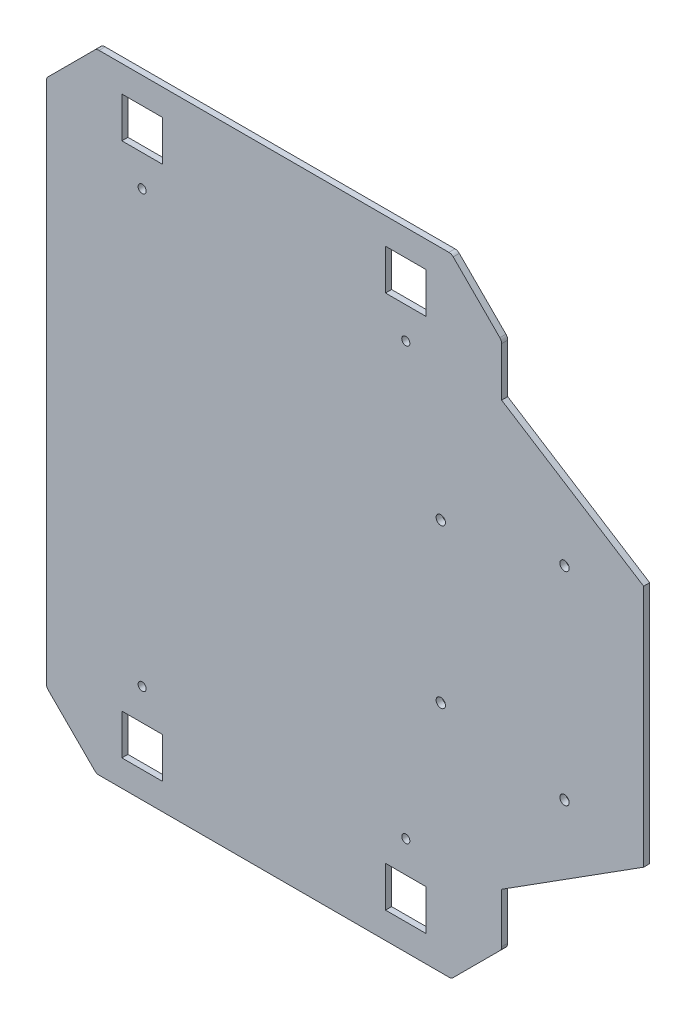
SolidWorks part; units mm, degrees
material "Pin"
ref_plane "Plan de dessus" through (0, 0, 0) normal (0, 0, 1) x (1, 0, 0)
ref_plane "Plan de droite" through (0, 0, 0) normal (0, 1, 0) x (1, 0, 0)
ref_plane "Plan de face" through (0, 0, 0) normal (1, 0, 0) x (0, 0, -1)
sketch "Esquisse1" plane through (0, 0, 0) normal (0, 0, 1) x (1, 0, 0)
  line L0 (0, 0) -> (-175, 0)
  line L1 (-175, 0) -> (-199.7487, 24.7487)
  line L2 (-199.7487, 24.7487) -> (-199.7487, 284.7487)
  line L3 (-199.7487, 284.7487) -> (-175, 309.4975)
  line L4 (-175, 309.4975) -> (0, 309.4975)
  line L5 (0, 309.4975) -> (24.7487, 284.7487)
  line L6 (24.7487, 284.7487) -> (24.7487, 24.7487)
  line L7 (24.7487, 24.7487) -> (0, 0)
  dimension "D1" = 260
  dimension "D2" = 35
  dimension "D3" = 135
  dimension "D4" = 175
extrude "Base" add sketch "Esquisse1" along normal blind 3
sketch "Esquisse2" plane through (0, 0, 3) normal (0, 0, 1) x (1, 0, 0)
  line L0 (-87.5, 309.4975) -> (-87.5, 0) construction
  line L5 (0, 309.4975) -> (-175, 309.4975) construction
  line L6 (-175, 0) -> (0, 0) construction
  line L7 (-199.7487, 154.7487) -> (24.7487, 154.7487) construction
  line L8 (-199.7487, 284.7487) -> (-199.7487, 24.7487) construction
  line L9 (24.7487, 24.7487) -> (24.7487, 284.7487) construction
  line L10 (-162.5, 13) -> (-142.5, 33) construction
  line L11 (-162.5, 276.4975) -> (-142.5, 276.4975)
  line L12 (-162.5, 276.4975) -> (-162.5, 296.4975)
  line L13 (-162.5, 296.4975) -> (-142.5, 296.4975)
  line L14 (-142.5, 276.4975) -> (-142.5, 296.4975)
  line L15 (-162.5, 276.4975) -> (-142.5, 296.4975) construction
  line L16 (-162.5, 296.4975) -> (-142.5, 276.4975) construction
  line L17 (-162.5, 33) -> (-142.5, 13) construction
  line L18 (-162.5, 13) -> (-142.5, 13)
  line L19 (-162.5, 33) -> (-162.5, 13)
  line L20 (-162.5, 33) -> (-142.5, 33)
  line L21 (-142.5, 33) -> (-142.5, 13)
  line L22 (-12.5, 13) -> (-32.5, 13)
  line L23 (-12.5, 33) -> (-32.5, 33)
  line L24 (-32.5, 33) -> (-32.5, 13)
  line L25 (-12.5, 33) -> (-32.5, 13) construction
  line L26 (-12.5, 13) -> (-32.5, 33) construction
  line L27 (-12.5, 33) -> (-12.5, 13)
  line L28 (-32.5, 276.4975) -> (-32.5, 296.4975)
  line L29 (-12.5, 276.4975) -> (-32.5, 296.4975) construction
  line L30 (-12.5, 296.4975) -> (-32.5, 276.4975) construction
  line L31 (-12.5, 276.4975) -> (-32.5, 276.4975)
  line L32 (-12.5, 276.4975) -> (-12.5, 296.4975)
  line L33 (-12.5, 296.4975) -> (-32.5, 296.4975)
  point P0 (-152.5, 286.4975)
  dimension "D1" = 20
  dimension "D2" = 65
  dimension "D3" = 23
extrude "Enlèv. mat.-Extru.1" cut sketch "Esquisse2" against normal through all
sketch "Esquisse4" plane through (0, 0, 3) normal (0, 0, 1) x (1, 0, 0)
  line L0 (-152.5, 276.4975) -> (-152.5, 260.9975) construction
  line L1 (-162.5, 276.4975) -> (-142.5, 276.4975) construction
  line L2 (-199.7487, 154.7487) -> (24.7487, 154.7487) construction
  line L3 (-199.7487, 284.7487) -> (-199.7487, 24.7487) construction
  line L4 (24.7487, 24.7487) -> (24.7487, 284.7487) construction
  line L5 (-87.5, 309.4975) -> (-87.5, 0) construction
  line L6 (0, 309.4975) -> (-175, 309.4975) construction
  line L7 (-175, 0) -> (0, 0) construction
  circle A0 centre (-152.5, 260.9975) radius 2
  circle A1 centre (-152.5, 48.5) radius 2
  circle A2 centre (-22.5, 260.9975) radius 2
  circle A3 centre (-22.5, 48.5) radius 2
  dimension "D2" = 4
  dimension "D1" = 15.5
extrude "Enlèv. mat.-Extru.4" cut sketch "Esquisse4" against normal blind 3
fillet "Congé1" radius 3 8 edges at (-199.7487, 24.7487, 1.5) (-175, 0, 1.5) (0, 0, 1.5) (24.7487, 24.7487, 1.5) (24.7487, 284.7487, 1.5) (0, 309.4975, 1.5) (-175, 309.4975, 1.5) (-199.7487, 284.7487, 1.5)
sketch "Esquisse6" plane through (0, 0, 3) normal (0, 0, 1) x (1, 0, 0)
  line L3 (24.7487, 25.9914) -> (24.7487, 283.5061) construction
  line L5 (24.7487, 214.9495) -> (24.7487, 94.548)
  line L7 (94.7487, 214.9495) -> (94.7487, 94.9495)
  line L8 (-199.7487, 283.5061) -> (-199.7487, 25.9914) construction
  line L9 (94.7487, 214.9495) -> (24.7487, 259.3691)
  line L10 (94.7487, 94.9495) -> (24.7487, 50.53)
  line L11 (24.7487, 259.3691) -> (24.7487, 214.9495)
  line L12 (24.7487, 50.53) -> (24.7487, 94.548)
  point P10 (-199.7487, 154.7487)
  point P11 (24.7487, 154.7487)
  dimension "D1" = 70
  dimension "D2" = 120
extrude "Boss.-Extru.2" add sketch "Esquisse6" against normal blind 3
sketch "Esquisse3" plane through (0, 0, 3) normal (0, 0, 1) x (1, 0, 0)
  line L0 (24.7487, 259.3691) -> (24.7487, 50.53) construction
  line L2 (89.7487, 154.1747) -> (-0.2513, 154.1747) construction
  line L3 (89.7487, 199.1747) -> (89.7487, 109.1747) construction
  line L4 (89.7487, 109.1747) -> (-0.2513, 109.1747) construction
  line L5 (-0.2513, 109.1747) -> (-0.2513, 199.1747) construction
  line L6 (-0.2513, 199.1747) -> (89.7487, 199.1747) construction
  line L7 (-199.6346, 154.1747) -> (-148.7423, 154.1747) construction
  line L10 (-199.5204, 24.8433) -> (-199.7487, 283.5061) construction
  circle A0 centre (-5.2513, 193.1747) radius 2.3
  circle A2 centre (55.7487, 204.1747) radius 2.3
  arc A4 (-199.7487, 25.9914) -> (-198.8701, 23.8701) centre (-196.7487, 25.9914) ccw construction
  circle A5 centre (-5.2513, 115.1747) radius 2.3
  circle A6 centre (55.7487, 104.1747) radius 2.3
  dimension "D5" = 4.6
  dimension "D10" = 4.6
  dimension "D1" = 90
  dimension "D2" = 90
  dimension "D3" = 65
  dimension "D6" = 5
  dimension "D7" = 6
  dimension "D8" = 34
  dimension "D9" = 5
extrude "trous lidar" cut sketch "Esquisse3" against normal blind 10
